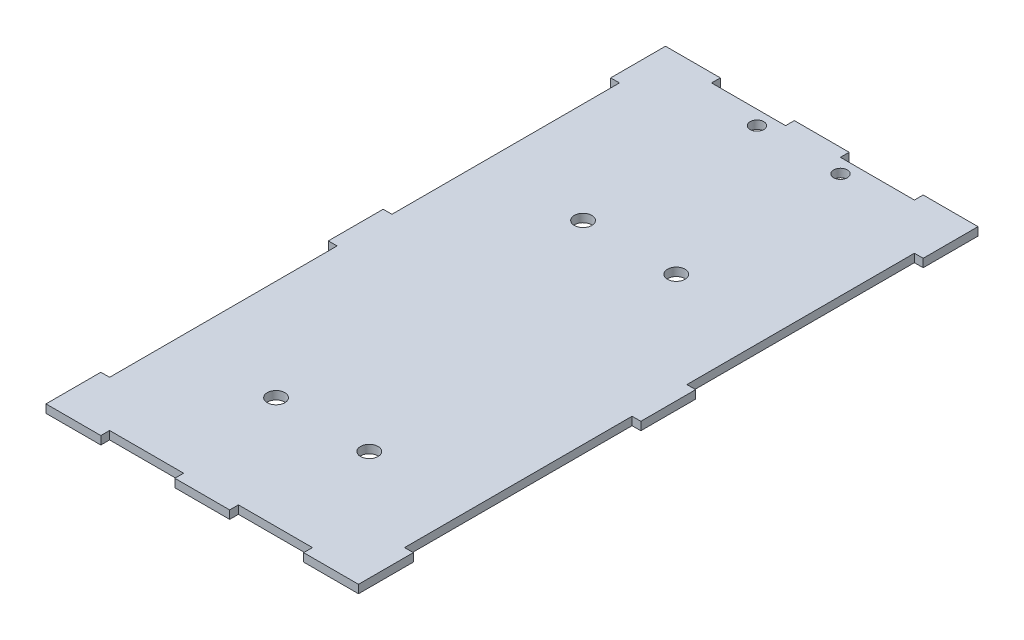
SolidWorks part; units mm, degrees
ref_plane "Front Plane" through (0, 0, 0) normal (0, 0, 1) x (1, 0, 0)
ref_plane "Top Plane" through (0, 0, 0) normal (0, 1, 0) x (1, 0, 0)
ref_plane "Right Plane" through (0, 0, 0) normal (1, 0, 0) x (0, 0, -1)
sketch "Sketch1" plane through (0, 0, 0) normal (0, 1, 0) x (1, 0, 0)
  line L0 (57, 0) -> (57, 10)
  line L5 (57, 10) -> (55.4, 10)
  line L6 (55.4, 10) -> (55.4, 51.5)
  line L7 (55.4, 51.5) -> (57, 51.5)
  line L8 (57, 51.5) -> (57, 61.5)
  line L9 (57, 61.5) -> (55.4, 61.5)
  line L10 (55.4, 61.5) -> (55.4, 103)
  line L11 (55.4, 103) -> (57, 103)
  line L12 (57, 103) -> (57, 113)
  line L13 (0, 0) -> (0, 10)
  line L14 (0, 10) -> (1.6, 10)
  line L15 (1.6, 10) -> (1.6, 51.5)
  line L16 (1.6, 51.5) -> (0, 51.5)
  line L17 (0, 51.5) -> (0, 61.5)
  line L18 (0, 61.5) -> (1.6, 61.5)
  line L19 (1.6, 61.5) -> (1.6, 103)
  line L20 (1.6, 103) -> (0, 103)
  line L21 (0, 103) -> (0, 113)
  line L22 (57, 113) -> (47, 113)
  line L23 (47, 113) -> (47, 111.4)
  line L24 (47, 111.4) -> (33.5, 111.4)
  line L25 (33.5, 111.4) -> (33.5, 113)
  line L26 (33.5, 113) -> (23.5, 113)
  line L27 (23.5, 113) -> (23.5, 111.4)
  line L28 (23.5, 111.4) -> (10, 111.4)
  line L29 (10, 111.4) -> (10, 113)
  line L30 (10, 113) -> (0, 113)
  line L31 (57, 0) -> (47, 0)
  line L32 (47, 0) -> (47, 1.6)
  line L33 (47, 1.6) -> (33.5, 1.6)
  line L34 (33.5, 1.6) -> (33.5, 0)
  line L35 (33.5, 0) -> (23.5, 0)
  line L36 (23.5, 0) -> (23.5, 1.6)
  line L37 (23.5, 1.6) -> (10, 1.6)
  line L38 (10, 1.6) -> (10, 0)
  line L39 (10, 0) -> (0, 0)
  circle A0 centre (20.88, 108.8) radius 1.25
  circle A1 centre (36.12, 108.8) radius 1.25
  circle A2 centre (20, 77.9646) radius 1.6
  circle A3 centre (37, 77.9646) radius 1.6
  circle A4 centre (20, 21.9646) radius 1.6
  circle A5 centre (37, 21.9646) radius 1.6
  point P22 (57, 5)
  dimension "D4" = 2.5
  dimension "D13" = 3.2
  dimension "D1" = 57
  dimension "D2" = 113
  dimension "D3" = 15.24
  dimension "D9" = 56
  dimension "D10" = 17
  dimension "D6" = 1.6
  dimension "D11" = 10
  dimension "D15" = 10
  dimension "D16" = 10
  dimension "D7" = 10
  dimension "D8" = 10
  dimension "D5" = 2.6
  dimension "D12" = 21.9646
  dimension "D14" = 13.5
extrude "Boss-Extrude1" add sketch "Sketch1" along normal blind 1.5
equation "\"margin\"= 0.2"
equation "\"height\"= 18"
equation "\"length\"= 113"
equation "\"tabwidth\"= 10"
equation "\"D11@Sketch1\"=\"tabwidth\""
equation "\"D16@Sketch1\"=\"tabwidth\""
equation "\"D15@Sketch1\"=\"tabwidth\""
equation "\"D7@Sketch1\"=\"tabwidth\""
equation "\"D8@Sketch1\"=\"tabwidth\""
equation "\"width\"= 57"
equation "\"thick\"= 1.5"
equation "\"D6@Sketch1\"=\"thick\"+(\"margin\"/2)"
equation "\"D1@Boss-Extrude1\"=\"thick\""
